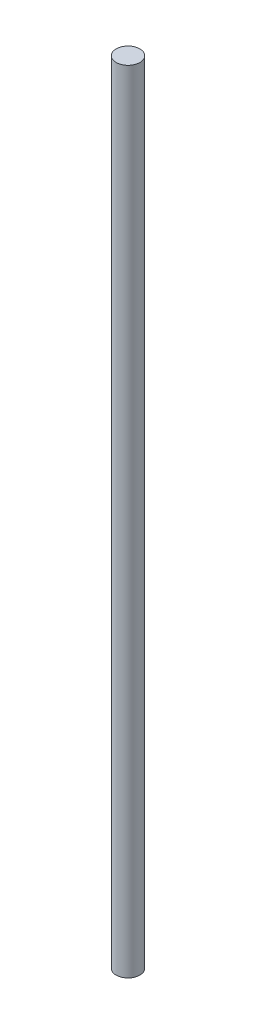
SolidWorks part; units mm, degrees
ref_plane "Front Plane" through (0, 0, 0) normal (0, 0, 1) x (1, 0, 0)
ref_plane "Top Plane" through (0, 0, 0) normal (0, 1, 0) x (1, 0, 0)
ref_plane "Right Plane" through (0, 0, 0) normal (1, 0, 0) x (0, 0, -1)
sketch "Sketch1" plane through (0, 0, 0) normal (0, 1, 0) x (1, 0, 0)
  circle A0 centre (0, 0) radius 1.5
  dimension "D1" = 3
extrude "Boss-Extrude1" add sketch "Sketch1" along normal blind 100.1
